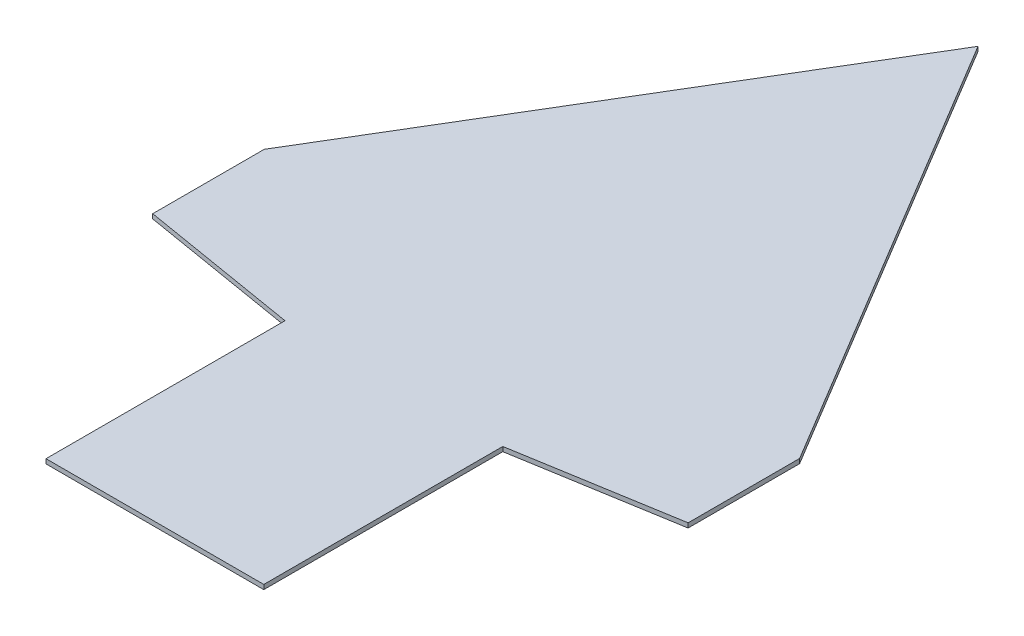
SolidWorks part; units mm, degrees
ref_plane "Front Plane" through (0, 0, 0) normal (0, 0, 1) x (1, 0, 0)
ref_plane "Top Plane" through (0, 0, 0) normal (0, 1, 0) x (1, 0, 0)
ref_plane "Right Plane" through (0, 0, 0) normal (1, 0, 0) x (0, 0, -1)
sketch "Sketch1" plane through (0, 0, 0) normal (0, 1, 0) x (1, 0, 0)
  line L6 (23.417, 69.5136) -> (23.417, -298.7864) construction
  line L18 (25.131, 82.2136) -> (21.7029, 82.2136)
  line L24 (-37.543, -266.5965) -> (-37.543, -400.3864)
  line L27 (-37.543, -400.3864) -> (84.377, -400.3864)
  line L28 (84.377, -400.3864) -> (84.377, -266.5965)
  line L82 (23.417, 60.3894) -> (-126.443, -189.3218)
  line L83 (-126.443, -189.3218) -> (-126.443, -251.7469)
  line L86 (-132.793, -250.6862) -> (-31.193, -267.6572) construction
  line L88 (179.627, -250.6862) -> (78.027, -267.6572) construction
  line L92 (173.277, -189.3218) -> (173.277, -251.7469)
  line L121 (23.417, 60.3894) -> (173.277, -189.3218)
  line L124 (23.417, 60.3894) -> (23.417, 60.3894)
  line L152 (23.417, 72.7296) -> (23.417, 72.7296)
  line L155 (-126.443, -251.7469) -> (-37.543, -266.5965)
  line L159 (173.277, -251.7469) -> (84.377, -266.5965)
  line L162 (-37.543, -273.0345) -> (-37.543, -400.3864) construction
  line L163 (84.377, -400.3864) -> (84.377, -273.0345) construction
  line L164 (-126.443, -189.3218) -> (-126.443, -245.3089) construction
  line L165 (173.277, -189.3218) -> (173.277, -245.3089) construction
  line L195 (-31.193, -267.6572) -> (-31.193, -394.0364) construction
  line L196 (-24.843, -262.2799) -> (-24.843, -387.6864) construction
  line L197 (71.677, -387.6864) -> (71.677, -262.2799) construction
  line L198 (78.027, -394.0364) -> (78.027, -267.6572) construction
  line L199 (-31.193, -394.0364) -> (78.027, -394.0364) construction
  line L200 (-24.843, -387.6864) -> (71.677, -387.6864) construction
  line L201 (-139.143, -256.0635) -> (-37.543, -273.0345) construction
  line L202 (185.977, -256.0635) -> (84.377, -273.0345) construction
  line L203 (23.417, 72.7296) -> (179.627, -187.5626) construction
  line L204 (25.131, 82.2136) -> (185.977, -185.8034) construction
  line L205 (21.7029, 82.2136) -> (-139.143, -185.8034) construction
  line L206 (23.417, 72.7296) -> (-132.793, -187.5626) construction
  line L207 (173.277, -245.3089) -> (71.677, -262.2799) construction
  line L208 (-126.443, -245.3089) -> (-24.843, -262.2799) construction
  line L209 (-132.793, -187.5626) -> (-132.793, -250.6862) construction
  line L210 (-139.143, -185.8034) -> (-139.143, -256.0635) construction
  line L211 (179.627, -187.5626) -> (179.627, -250.6862) construction
  line L212 (185.977, -185.8034) -> (185.977, -256.0635) construction
  dimension "D1" = 12.7
  dimension "D4" = 6.35
extrude "Boss-Extrude1" add sketch "Sketch1" along normal blind 2.54
